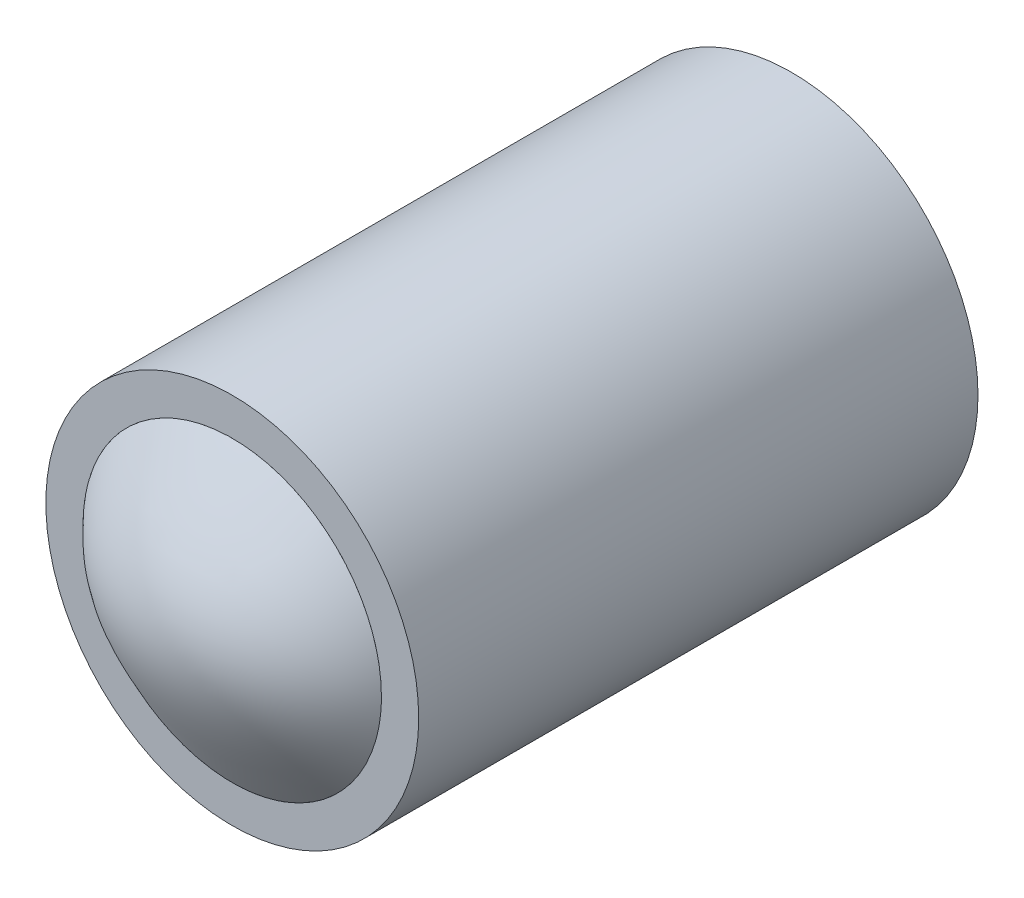
SolidWorks part; units mm, degrees
ref_plane "Front Plane" through (0, 0, 0) normal (0, 0, 1) x (1, 0, 0)
ref_plane "Top Plane" through (0, 0, 0) normal (0, 1, 0) x (1, 0, 0)
ref_plane "Right Plane" through (0, 0, 0) normal (1, 0, 0) x (0, 0, -1)
sketch "Sketch1" plane through (0, 0, 0) normal (0, 0, 1) x (1, 0, 0)
  circle A0 centre (0, 0) radius 5
  dimension "D1" = 10
extrude "Boss-Extrude1" add sketch "Sketch1" against normal blind 15 contours A0
shell "Shell5" thickness 1
sketch "Sketch4" plane through (0, 0, 0) normal (0, 1, 0) x (1, 0, 0)
  line L0 (-4, 0) -> (4, 0) construction
  arc A0 (4, 0) -> (-4, 0) centre (0, 3.5802) cw
surface "Surface-Fill4"
